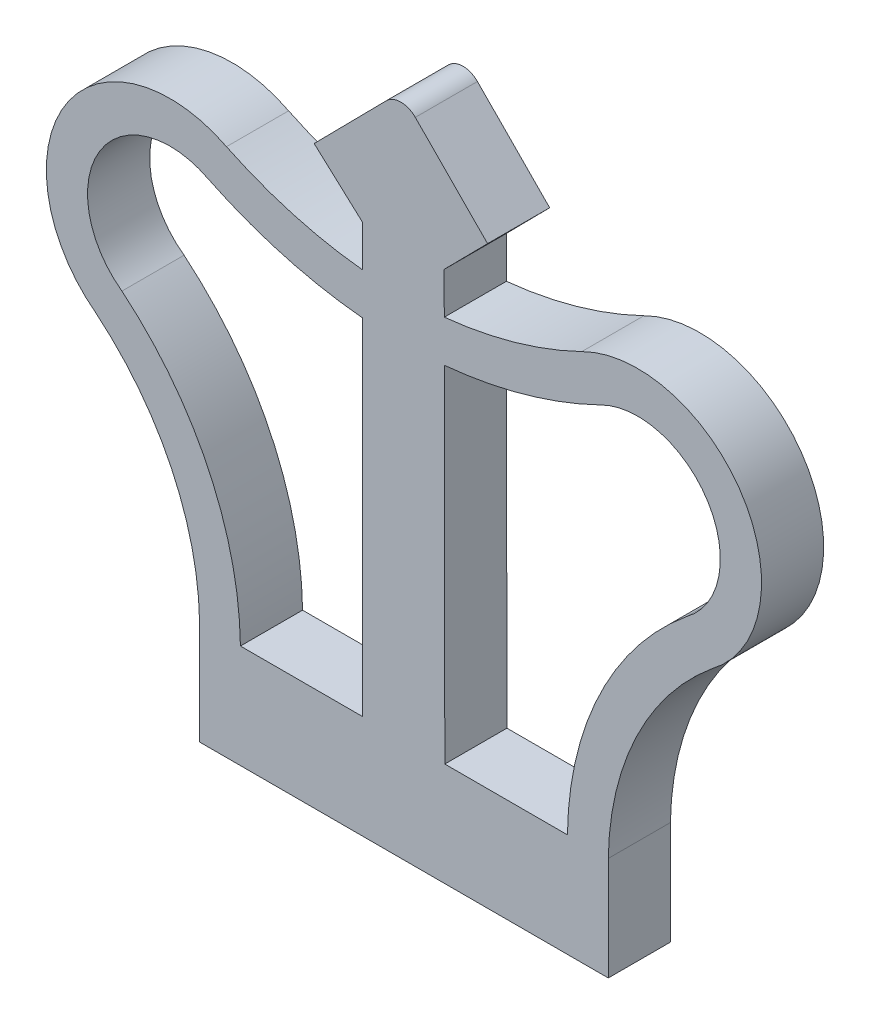
SolidWorks part; units mm, degrees
ref_plane "Alzado" through (0, 0, 0) normal (0, 0, 1) x (1, 0, 0)
ref_plane "Planta" through (0, 0, 0) normal (0, 1, 0) x (1, 0, 0)
ref_plane "Vista lateral" through (0, 0, 0) normal (1, 0, 0) x (0, 0, -1)
sketch "Model" plane through (0, 0, 0) normal (0, 0, 1) x (1, 0, 0)
  line L0 (52.1263, 0.6914) -> (71.8597, 0.6914)
  line L1 (59.9906, 22.3592) -> (59.9906, 5.6914)
  line L2 (59.9906, 5.6914) -> (54.0982, 5.6914)
  line L3 (63.9663, 5.6914) -> (63.9429, 22.3545)
  line L4 (69.8867, 5.6914) -> (63.9663, 5.6914)
  line L5 (59.9906, 26.3627) -> (59.9906, 24.3685)
  line L6 (57.6581, 28.4841) -> (59.9906, 26.3627)
  line L7 (61.1465, 32.0196) -> (57.6581, 28.4841)
  line L8 (66.0303, 28.4841) -> (62.5419, 32.0196)
  line L9 (63.9372, 26.3627) -> (66.0303, 28.4841)
  line L10 (63.94, 24.363) -> (63.9372, 26.3627)
  line L11 (71.8597, 0.6914) -> (71.8597, 5.6914)
  line L12 (52.1263, 0.6914) -> (52.1263, 5.6914)
  arc A0 (62.5419, 32.0196) -> (61.1465, 32.0196) centre (61.8442, 31.3219) ccw
  arc A1 (63.94, 24.363) -> (70.5788, 26.2433) centre (61.9211, 44.1513) ccw
  arc A2 (76.8649, 16.1276) -> (70.5788, 26.2433) centre (73.2817, 20.9119) ccw
  arc A3 (76.8649, 16.1276) -> (71.8597, 5.6914) centre (85.6707, 5.4859) ccw
  arc A4 (50.3911, 12.1913) -> (47.1211, 16.1276) centre (38.3153, 5.4859) ccw
  arc A5 (53.4244, 26.2343) -> (47.1211, 16.1276) centre (50.7042, 20.9119) ccw
  arc A6 (53.4244, 26.2343) -> (59.9906, 24.3685) centre (62.0637, 44.1512) ccw
  arc A7 (52.1263, 5.6914) -> (50.3911, 12.1913) centre (38.3153, 5.4859) ccw
  arc A8 (54.0982, 5.6914) -> (48.3766, 17.6736) centre (38.2889, 5.4996) ccw
  arc A9 (52.5408, 24.4457) -> (48.3766, 17.6736) centre (50.7017, 20.9102) ccw
  arc A10 (52.5408, 24.4457) -> (59.9906, 22.3592) centre (62.0697, 44.1259) ccw
  arc A11 (63.9429, 22.3545) -> (71.4599, 24.4535) centre (61.9152, 44.1259) ccw
  arc A12 (75.6471, 17.7018) -> (71.4599, 24.4535) centre (73.284, 20.9105) ccw
  arc A13 (75.6471, 17.7018) -> (69.8867, 5.6914) centre (85.689, 5.499) ccw
extrude "Saliente-Extruir1" add sketch "Model" along normal blind 3
